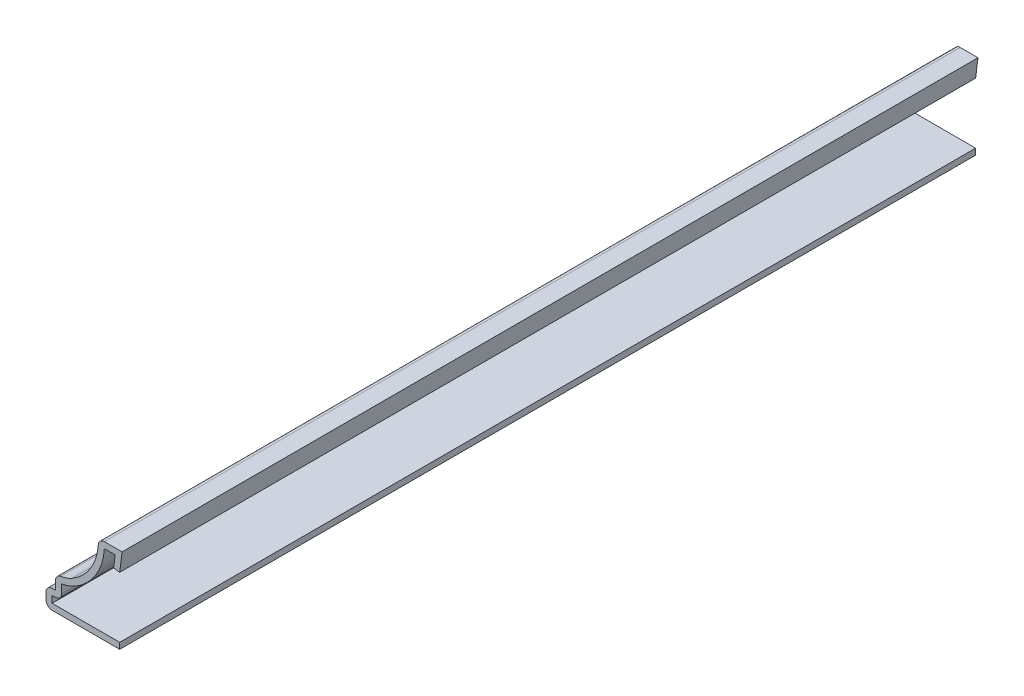
SolidWorks part; units mm, degrees
ref_plane "Front Plane" through (0, 0, 0) normal (0, 0, 1) x (1, 0, 0)
ref_plane "Top Plane" through (0, 0, 0) normal (0, 1, 0) x (1, 0, 0)
ref_plane "Right Plane" through (0, 0, 0) normal (1, 0, 0) x (0, 0, -1)
sketch "Sketch1" plane through (0, 0, 0) normal (0, 0, 1) x (1, 0, 0)
  line L0 (0, 0) -> (0, 14.2875) construction
  line L1 (-0.3969, 11.1374) -> (0, 14.2875)
  line L2 (0, 14.2875) -> (-3.9688, 14.2875)
  line L3 (-0.3969, 0) -> (-12.7, 0)
  line L4 (-12.7, 0) -> (-12.7, 3.175)
  line L5 (-12.7, 3.175) -> (-11.1125, 3.175)
  line L6 (-11.1125, 3.175) -> (-11.1125, 5.5562)
  arc A0 (-3.9688, 14.2875) -> (-8.352, 6.2905) centre (-12.6899, 13.8679) cw
  arc A1 (-11.1125, 5.5562) -> (-8.352, 6.2905) centre (-11.1125, 11.1125) ccw
  point P12 (0, 0)
  point P13 (0, 0)
  point P14 (-5.0729, 9.6336)
  point P15 (0, 0)
  dimension "D10" = 8.7312
  dimension "D11" = 5.5562
  dimension "D1" = 14.2875
  dimension "D2" = 12.7
  dimension "D3" = 12.3031
  dimension "D4" = 3.175
  dimension "D5" = 2.3813
  dimension "D6" = 1.5875
  dimension "D7" = 3.9688
  dimension "D8" = 3.175
  dimension "D9" = 0.3969
extrude "Extrude-Thin1" add sketch "Sketch1" against normal blind 142.875 thin thin type one direction wall 1.016
fillet "Fillet1" radius 1.016 5 edges at (-12.7, 0, -71.4375) (-12.7, 3.175, -71.4375) (-10.0965, 2.159, -71.4375) (-11.1125, 5.5563, -71.4375) (-3.9688, 14.2875, -71.4375)
